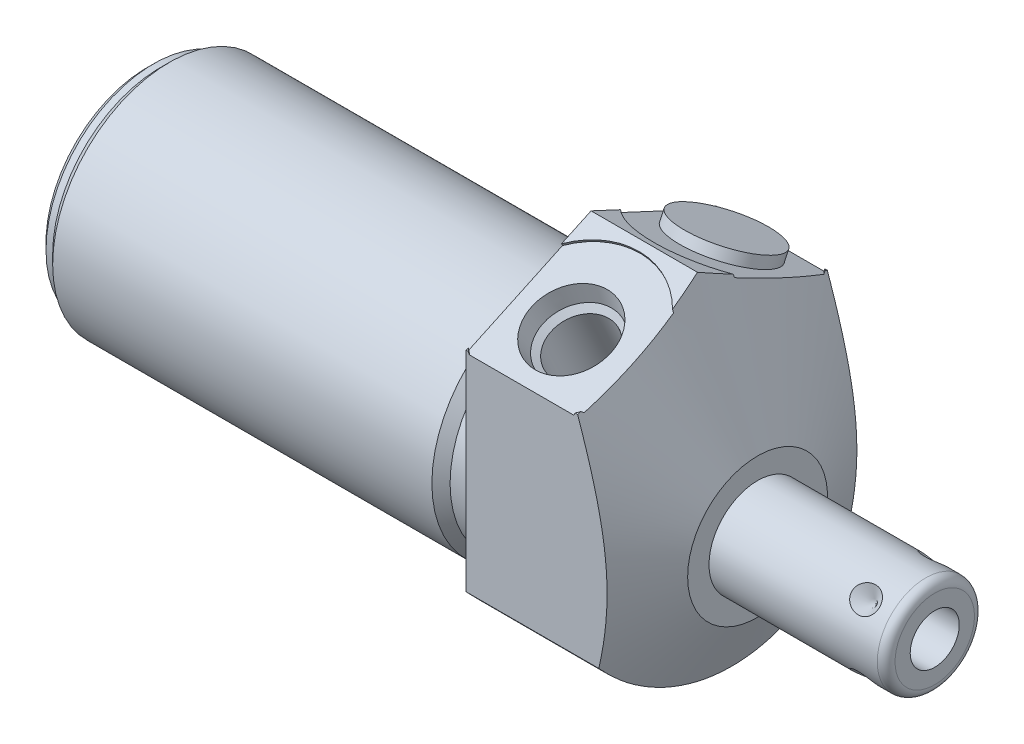
SolidWorks part; units mm, degrees
material "Alloy Steel"
ref_plane "Front Plane" through (0, 0, 0) normal (0, 0, 1) x (1, 0, 0)
ref_plane "Top Plane" through (0, 0, 0) normal (0, 1, 0) x (1, 0, 0)
ref_plane "Right Plane" through (0, 0, 0) normal (1, 0, 0) x (0, 0, -1)
ref_plane "Plane1" through (0, 0, 0) normal (1, 0, 0) x (0, 0, -1)
sketch "Sketch1" plane through (0, 0, 0) normal (1, 0, 0) x (0, 0, -1)
  circle A0 centre (0, 0) radius 19.05
  dimension "D1" = 38.1
extrude "Extrude1" add sketch "Sketch1" along normal blind 19.05 and the other way blind 50.8
ref_plane "Plane2" through (0, 0, 0) normal (1, 0, 0) x (0, 0, -1)
sketch "Sketch2" plane through (0, 0, 0) normal (1, 0, 0) x (0, 0, -1)
  line L0 (-14.6964, -4.7498) -> (14.6964, -4.7498) construction
  circle A0 centre (0, -4.7498) radius 13.3604
  circle A1 centre (0, 0) radius 19.05 construction
  circle A2 centre (0, 0) radius 19.05
  dimension "D1" = 26.7208
  dimension "D2" = 4.7498
extrude "Cut-Extrude1" cut sketch "Sketch2" against normal up to next
ref_plane "Plane4" through (0, 0, 0) normal (-1, 0, 0) x (0, 0, 1)
sketch "Sketch4" plane through (0, 0, 0) normal (-1, 0, 0) x (0, 0, 1)
  line L0 (14.2875, -12.6004) -> (14.2875, 11.3448)
  line L1 (14.2875, 11.3448) -> (0, 18.0071)
  line L2 (-14.2875, -12.6004) -> (-14.2875, 11.3448)
  line L3 (-14.2875, 11.3448) -> (0, 18.0071)
  line L4 (0, -20.9029) -> (0, 19.86) construction
  circle A0 centre (0, 0) radius 19.05 construction
  arc A1 (14.2875, -12.6004) -> (-14.2875, -12.6004) centre (0, 0) ccw
  dimension "D1" = 28.575
  dimension "D2" = 65
  dimension "D3" = 11.3448
extrude "Cut-Extrude3" cut sketch "Sketch4" against normal up to next
ref_plane "Plane6" through (0, 0, 0) normal (0, 0, 1) x (1, 0, 0)
sketch "Sketch6" plane through (0, 0, 0) normal (0, 0, 1) x (1, 0, 0)
  line L0 (12.1692, 18.0071) -> (19.05, 3.2512)
  line L1 (1.9872, -4.7498) -> (19.8625, -4.7498) construction
  line L2 (-50.8, -4.7498) -> (0, -4.7498) construction
  line L3 (19.05, 18.0071) -> (19.05, 11.3448) construction
  line L4 (19.05, 3.2512) -> (19.05, 18.0071)
  line L5 (19.05, 18.0071) -> (12.1692, 18.0071)
  line L6 (19.05, 18.0071) -> (0, 18.0071) construction
  dimension "D1" = 8.001
  dimension "D2" = 25
revolve "Cut-Revolve2" cut sketch "Sketch6" angle 360 about L1
ref_plane "Plane7" through (6.35, 13.7124, 8.6091) normal (1, 0, 0) x (0, 0.4226, -0.9063)
sketch "S2D0002" plane through (6.35, 13.7124, 8.6091) normal (1, 0, 0) x (0, 0.4226, -0.9063)
  line L0 (0, 0) -> (4.5466, 0)
  line L1 (4.5466, 0) -> (4.1066, -2.0701)
  line L2 (4.1066, -2.0701) -> (3.4544, -2.7223)
  line L3 (3.4544, -2.7223) -> (3.4544, -12.192)
  line L4 (3.4544, -12.192) -> (0, -12.192)
  line L5 (0, -12.192) -> (0, 0)
  line L6 (0, -12.8016) -> (0, 0.6096) construction
  dimension "D1" = 12.192
revolve "Cut-Revolve3" cut sketch "S2D0002" angle 360 about L6
ref_plane "Plane8" through (6.35, 13.7124, -8.6091) normal (1, 0, 0) x (0, -0.4226, -0.9063)
sketch "Sketch19" plane through (0, 14.791, 6.8971) normal (0, 0.9063, 0.4226) x (1, 0, 0)
  circle A0 centre (6.35, -2.0074) radius 8.6614
  dimension "D1" = 17.3228
extrude "Cut-Extrude4" cut sketch "Sketch19" against normal blind 0.254
sketch "Sketch8" plane through (6.35, 13.7124, -8.6091) normal (1, 0, 0) x (0, -0.4226, -0.9063)
  line L0 (0, 0) -> (4.5466, 0)
  line L1 (4.5466, 0) -> (4.1066, -2.0701)
  line L2 (4.1066, -2.0701) -> (3.4544, -2.7223)
  line L3 (3.4544, -2.7223) -> (3.4544, -12.192)
  line L4 (3.4544, -12.192) -> (0, -12.192)
  line L5 (0, -12.192) -> (0, 0)
  line L6 (0, -12.8016) -> (0, 0.6096) construction
  dimension "D1" = 12.192
revolve "Cut-Revolve4" cut sketch "Sketch8" angle 360 about L6
sketch "Sketch20" plane through (0, 14.791, -6.8971) normal (0, 0.9063, -0.4226) x (1, 0, 0)
  circle A0 centre (6.35, 2.0074) radius 8.6614
  dimension "D1" = 17.3228
extrude "Cut-Extrude5" cut sketch "Sketch20" against normal blind 0.254
ref_plane "Plane10" through (0, 0, 0) normal (0, 0, 1) x (1, 0, 0)
sketch "Sketch10" plane through (0, 0, 0) normal (0, 0, 1) x (1, 0, 0)
  line L0 (0, 8.6106) -> (0, 7.5692)
  line L1 (0, 7.5692) -> (-3.81, 7.5692)
  line L2 (-3.81, 7.5692) -> (-4.8514, 8.6106)
  line L3 (-5.094, -4.7498) -> (0.2426, -4.7498) construction
  line L4 (0, 8.6106) -> (-4.8514, 8.6106)
  line L5 (-50.8, -4.7498) -> (0, -4.7498) construction
  line L6 (0, 8.6106) -> (-50.8, 8.6106) construction
  line L7 (0, 11.3448) -> (0, -12.6004) construction
  dimension "D1" = 24.638
  dimension "D2" = 3.81
  dimension "D3" = 45
revolve "Cut-Revolve6" cut sketch "Sketch10" angle 360 about L3
ref_plane "Plane12" through (0, 0, 0) normal (0, 0, 1) x (1, 0, 0)
sketch "Sketch12" plane through (0, 0, 0) normal (0, 0, 1) x (1, 0, 0)
  line L0 (-50.8, 8.6106) -> (-50.8, 7.5692)
  line L1 (-50.8, 7.5692) -> (-49.276, 7.5692)
  line L2 (-49.276, 7.5692) -> (-48.2346, 8.6106)
  line L3 (-50.9283, -4.7498) -> (-48.1063, -4.7498) construction
  line L4 (-50.8, 8.6106) -> (-48.2346, 8.6106)
  line L5 (-50.8, -4.7498) -> (-4.8514, -4.7498) construction
  line L6 (-4.8514, 8.6106) -> (-50.8, 8.6106) construction
  line L7 (-50.8, 8.6106) -> (-50.8, -18.1102) construction
  dimension "D1" = 24.638
  dimension "D2" = 1.524
  dimension "D3" = 45
revolve "Cut-Revolve8" cut sketch "Sketch12" angle 360 about L3
chamfer "Chamfer1" distance 0.762 angle 45 1 edges at (-50.8, -4.7498, 12.319)
ref_plane "Plane13" through (0, 0, 0) normal (0, 0, 1) x (0, -1, 0)
sketch "Sketch13" plane through (0, 0, 0) normal (0, 0, 1) x (0, -1, 0)
  line L0 (4.7498, 19.05) -> (4.7498, 39.3192)
  line L1 (4.7498, 39.3192) -> (9.2901, 39.3192)
  line L2 (10.306, 38.3032) -> (10.306, 19.05)
  line L3 (10.306, 19.05) -> (4.7498, 19.05)
  line L4 (4.7498, 18.0365) -> (4.7498, 40.3327) construction
  line L5 (4.7498, -48.2346) -> (4.7498, -4.8514) construction
  line L6 (12.7508, 19.05) -> (-3.2512, 19.05) construction
  line L7 (-11.3448, 0) -> (12.6004, 0) construction
  arc A0 (10.306, 38.3032) -> (9.2901, 39.3192) centre (9.2901, 38.3032) ccw
  dimension "D2" = 1.016
  dimension "D1" = 39.3192
  dimension "D3" = 11.1125
revolve "Revolve1" add sketch "Sketch13" angle 360 about L4
ref_plane "Plane14" through (39.3192, -7.5565, 0) normal (0, 0, 1) x (0, -1, 0)
sketch "S2D0001" plane through (39.3192, -7.5565, 0) normal (0, 0, 1) x (0, -1, 0)
  line L0 (0, 0) -> (0, -10.16)
  line L1 (0, -10.16) -> (-2.8067, -11.8464)
  line L2 (0, 0) -> (-2.8067, 0)
  line L3 (-2.8067, 0) -> (-2.8067, -11.8464)
  line L4 (-2.8067, -12.4388) -> (-2.8067, 0.5923) construction
  line L5 (-2.8067, -1.016) -> (-2.8067, -20.2692) construction
  line L6 (1.7336, 0) -> (-7.347, 0) construction
  dimension "D1" = 5.6134
  dimension "D2" = 59
  dimension "D3" = 10.16
revolve "Cut-Revolve9" cut sketch "S2D0001" angle 360 about L4
ref_plane "Plane15" through (19.05, 14.5608, -6.7898) normal (0, -0.9063, 0.4226) x (0, -0.4226, -0.9063)
sketch "Sketch15" plane through (19.05, 14.5608, -6.7898) normal (0, -0.9063, 0.4226) x (0, -0.4226, -0.9063)
  circle A0 centre (2.0074, -12.7) radius 5.3086
extrude "Extrude2" add sketch "Sketch15" against normal blind 1.27
ref_plane "Plane16" through (35.3568, -10.306, 0) normal (0, 0, 1) x (-1, 0, 0)
ref_plane "Plane17" through (0, -2.3749, -2.3749) normal (0, 0.7071, 0.7071) x (-1, 0, 0)
sketch "Sketch16" plane through (35.3568, -0.8209, -3.9289) normal (0, -0.7071, -0.7071) x (-1, 0, 0)
  line L0 (0, 0) -> (1.5875, 0)
  line L1 (1.5875, 0) -> (0, -1.5875)
  line L2 (0, 0) -> (0, -1.5875)
  line L3 (0, -3.4788) -> (0, 0.0794) construction
  line L4 (-3.9624, -1.016) -> (-3.9624, -10.0965) construction
  line L5 (16.3068, 0) -> (-2.9464, 0) construction
  dimension "D1" = 3.9624
  dimension "D2" = 3.175
  dimension "D3" = 45
revolve "Cut-Revolve10" cut sketch "Sketch16" angle 360 about L3
pattern_circular "CirPattern1" count 4 over 360 about axis through (18.0365, -4.7498, 0) along (-1, 0, 0) of "Cut-Revolve10"
